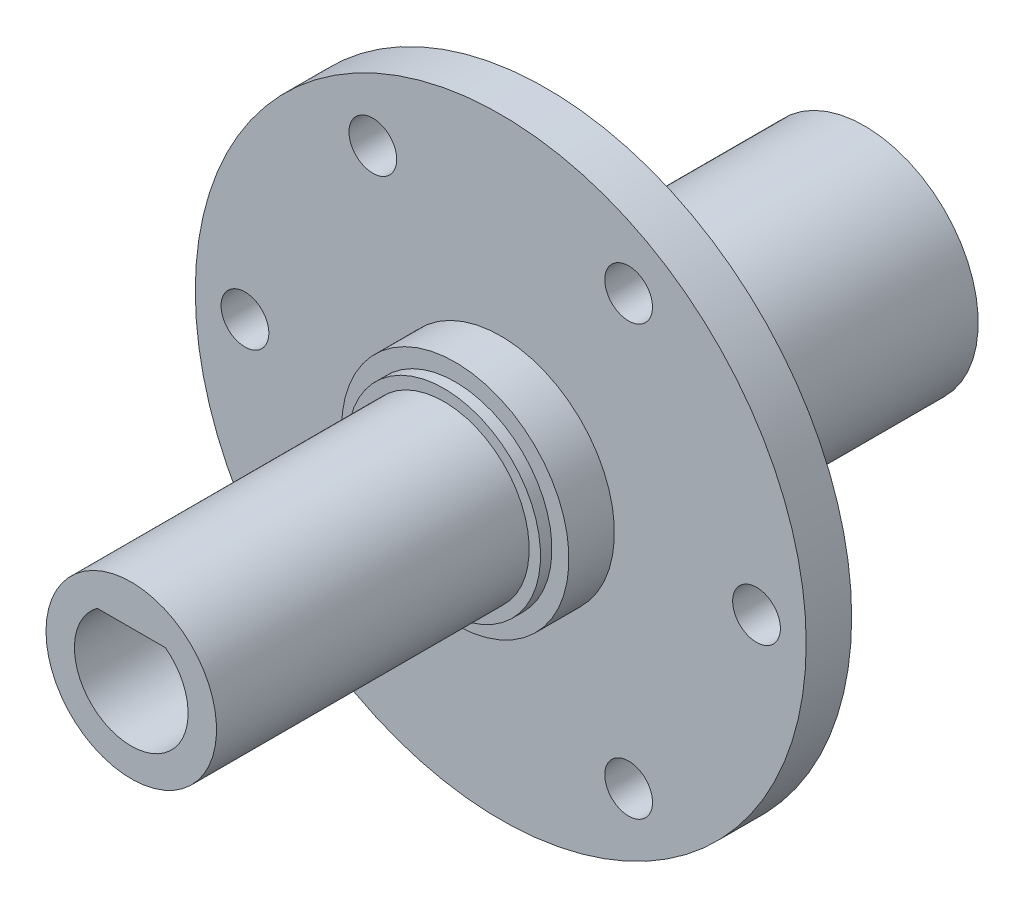
SolidWorks part; units mm, degrees
ref_plane "前视基准面" through (0, 0, 0) normal (0, 0, 1) x (1, 0, 0)
ref_plane "上视基准面" through (0, 0, 0) normal (0, 1, 0) x (1, 0, 0)
ref_plane "右视基准面" through (0, 0, 0) normal (1, 0, 0) x (0, 0, -1)
sketch "草图2" plane through (0, 0, 0) normal (0, 1, 0) x (1, 0, 0)
  line L0 (-21.7422, 43.9843) -> (-18.7422, 43.9843)
  line L1 (-21.7422, 43.9843) -> (-21.7422, 15.9843)
  line L2 (-21.7422, 15.9843) -> (-38.6122, 15.9843)
  line L3 (-38.6122, 15.9843) -> (-38.6122, 11.9843)
  line L4 (-38.6122, 11.9843) -> (-21.7422, 11.9843)
  line L5 (-21.7422, 11.9843) -> (-21.7422, 7.9843)
  line L6 (-21.7422, 7.9843) -> (-20.2422, 7.9843)
  line L7 (-20.2422, 7.9843) -> (-20.2422, 6.9843)
  line L8 (-20.2422, 6.9843) -> (-19.2422, 6.9843)
  line L9 (-19.2422, 6.9843) -> (-19.2422, -20.5157)
  line L10 (-19.2422, -20.5157) -> (-11.7422, -20.5157)
  line L11 (-11.7422, 18.9793) -> (-11.7422, -20.5157)
  line L12 (-18.7422, 43.9843) -> (-18.7422, 23.0343)
  line L14 (-11.7422, 18.9793) -> (-18.7422, 23.0343)
revolve "旋转1" add sketch "草图2" angle 360 about L11
sketch "草图3" plane through (0, 0, 20.5157) normal (0, 0, 1) x (1, 0, 0)
  line L1 (-11.7422, 4) -> (-14.7422, 4)
  line L2 (-11.7422, 4) -> (-8.7422, 4)
  arc A0 (-14.7422, 4) -> (-8.7422, 4) centre (-11.7422, 0) ccw
extrude "切除-拉伸1" cut sketch "草图3" against normal blind 13.4 contours A0 L2 L1
sketch "草图4" plane through (0, 0, -11.9843) normal (0, 0, 1) x (1, 0, 0)
  circle A0 centre (-0.4922, -18.86) radius 2.1
  circle A1 centre (10.7578, 0) radius 2.1
  circle A2 centre (-22.9922, -18.86) radius 2.1
  circle A3 centre (-34.2422, 0) radius 2.1
  circle A4 centre (-22.9922, 18.86) radius 2.1
  circle A5 centre (-0.4922, 18.86) radius 2.1
extrude "切除-拉伸2" cut sketch "草图4" against normal blind 13.4
